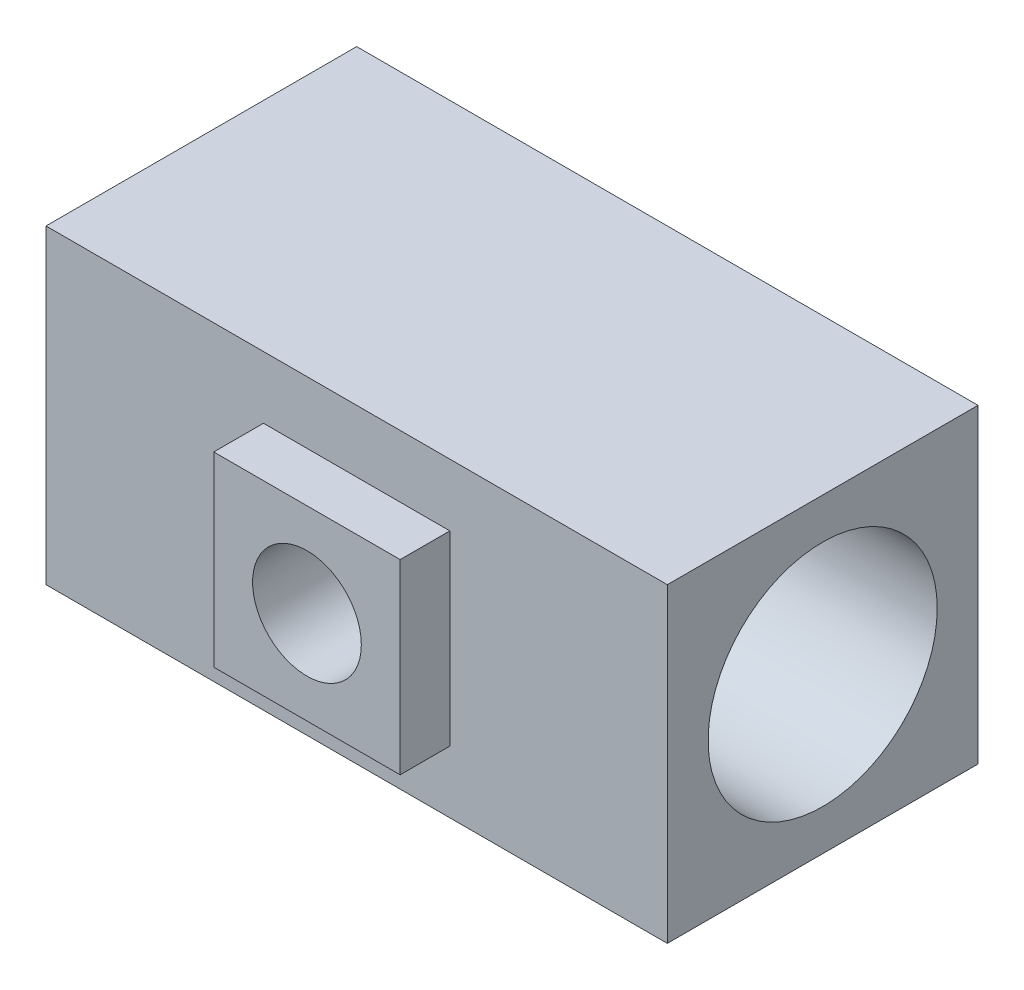
SolidWorks part; units mm, degrees
material "6061 Alloy"
ref_plane "X-Y Datum" through (0, 0, 0) normal (0, 0, 1) x (1, 0, 0)
ref_plane "X-Z Datum" through (0, 0, 0) normal (0, 1, 0) x (1, 0, 0)
ref_plane "Y-Z Datum" through (0, 0, 0) normal (1, 0, 0) x (0, 0, -1)
sketch "Sketch2" plane through (0, 0, 0) normal (0, 1, 0) x (1, 0, 0)
  line L1 (-31.75, -15.875) -> (31.75, -15.875)
  line L2 (-31.75, -15.875) -> (-31.75, 15.875)
  line L3 (-31.75, 15.875) -> (31.75, 15.875)
  line L4 (31.75, -15.875) -> (31.75, 15.875)
  line L5 (-31.75, -15.875) -> (31.75, 15.875) construction
  line L6 (-31.75, 15.875) -> (31.75, -15.875) construction
  point P0 (0, 0)
  dimension "D1" = 31.75
  dimension "D2" = 63.5
extrude "Boss-Extrude1" add sketch "Sketch2" along normal blind 31.75
hole_wizard "59/64 (0.92188) Diameter Hole1" positions "Sketch7" profile "Sketch6" hole size "59/64" standard "ANSI Inch" end condition through all
sketch "Sketch7" plane through (31.75, 0, 0) normal (1, 0, 0) x (0, 0, -1)
  line L0 (-15.875, 31.75) -> (15.875, 0)
  point P0 (0, 15.875)
sketch "Sketch6" plane through (31.75, 15.875, 0) normal (0, 1, 0) x (0, 0, -1)
  line L0 (0, 0) -> (0, 63.5)
  line L1 (0, 63.5) -> (11.7079, 63.5)
  line L2 (11.7079, 63.5) -> (11.7079, 0)
  line L5 (11.7079, 0) -> (0, 0)
  line L11 (0, -6.35) -> (0, 107.95) construction
  dimension "Thru Hole Dia." = 23.4158
  dimension "Thru Hole Depth" = 63.5
sketch "Sketch10" plane through (0, 0, 15.875) normal (0, 0, 1) x (1, 0, 0)
  line L0 (-31.75, 31.75) -> (31.75, 0)
  line L2 (-9.525, 6.35) -> (9.525, 6.35)
  line L3 (-9.525, 6.35) -> (-9.525, 25.4)
  line L4 (-9.525, 25.4) -> (9.525, 25.4)
  line L5 (9.525, 6.35) -> (9.525, 25.4)
  line L6 (-9.525, 6.35) -> (9.525, 25.4) construction
  line L7 (-9.525, 25.4) -> (9.525, 6.35) construction
  point P4 (0, 15.875)
  dimension "D1" = 19.05
  dimension "D2" = 19.05
extrude "Boss-Extrude2" add sketch "Sketch10" along normal blind 5.08 contours L2 L5 L0 L3 | L0 L5 L4 L3
hole_wizard "7/16 (0.4375) Diameter Hole1" positions "Sketch11" profile "Sketch12" hole size "7/16" standard "ANSI Inch"
sketch "Sketch11" plane through (0, 0, 20.955) normal (0, 0, 1) x (1, 0, 0)
  line L0 (-9.525, 25.4) -> (9.525, 6.35)
  point P0 (0, 15.875)
sketch "Sketch12" plane through (0, 15.875, 20.955) normal (1, 0, 0) x (0, -1, 0)
  line L0 (0, 0) -> (0, 28.7385)
  line L1 (0, 28.7385) -> (5.5562, 25.4)
  line L2 (5.5562, 25.4) -> (5.5562, 0)
  line L5 (5.5562, 0) -> (0, 0)
  line L10 (0, 28.7385) -> (-5.5563, 25.4) construction
  line L11 (0, -6.35) -> (0, 107.95) construction
  dimension "Hole Dia." = 11.1125
  dimension "Hole Depth" = 25.4
  dimension "Drill Angle" = 118
thread "Thread1" [suppressed] pitch 1.8143 start angle 0, offset 0, length 15.875, pitch 1.8143, diameter 23.4158
ref_plane "Plane1" through (31.75, 15.875, 11.7079) normal (0, -1, 0) x (0, 0, 1)
sketch "Thread Profile1" plane through (31.75, 15.875, 11.7079) normal (0, -1, 0) x (0, 0, 1)
  line L0 (0, 0) -> (0, 1.8143) construction
  line L1 (0, 0) -> (0.982, 0.567)
  line L2 (0.982, 0.567) -> (0.982, 0.7937)
  line L3 (0.982, 0.7937) -> (0, 1.3607)
  line L4 (0.982, 0.6804) -> (0, 0.6804) construction
  line L11 (0, 0) -> (0, 1.3607)
  point P2 (0, 0)
  dimension "Pitch" = 1.8143
  dimension "Profile_Angle" = 60
  dimension "Profile_Land" = 0.2268
  dimension "Profile_Height" = 0.982
thread "Thread2" [suppressed] pitch 1.8143 start angle 0, offset 0, length 15.875, pitch 1.8143, diameter 23.4158
ref_plane "Plane2" through (-31.75, 15.875, -11.7079) normal (0, -1, 0) x (0, 0, -1)
sketch "Thread Profile2" plane through (-31.75, 15.875, -11.7079) normal (0, -1, 0) x (0, 0, -1)
  line L0 (0, 0) -> (0, 1.8143) construction
  line L1 (0, 0) -> (0.982, 0.567)
  line L2 (0.982, 0.567) -> (0.982, 0.7937)
  line L3 (0.982, 0.7937) -> (0, 1.3607)
  line L4 (0.982, 0.6804) -> (0, 0.6804) construction
  line L11 (0, 0) -> (0, 1.3607)
  point P2 (0, 0)
  dimension "Pitch" = 1.8143
  dimension "Profile_Angle" = 60
  dimension "Profile_Land" = 0.2268
  dimension "Profile_Height" = 0.982
thread "Thread4" [suppressed] pitch 1.8143 start angle 0, offset 0, length 0, pitch 1.8143, diameter 11.1125
ref_plane "Plane4" through (-5.5562, 15.875, 20.955) normal (0, -1, 0) x (-1, 0, 0)
sketch "Thread Profile4" plane through (-5.5562, 15.875, 20.955) normal (0, -1, 0) x (-1, 0, 0)
  line L0 (0, 0) -> (0, 1.8143) construction
  line L1 (0, 0) -> (0.982, 0.567)
  line L2 (0.982, 0.567) -> (0.982, 0.7937)
  line L3 (0.982, 0.7937) -> (0, 1.3607)
  line L4 (0.982, 0.6804) -> (0, 0.6804) construction
  line L11 (0, 0) -> (0, 1.3607)
  point P2 (0, 0)
  dimension "Pitch" = 1.8143
  dimension "Profile_Angle" = 60
  dimension "Profile_Land" = 0.2268
  dimension "Profile_Height" = 0.982
sketch "Sketch13" plane through (-31.75, 0, 0) normal (-1, 0, 0) x (0, 0, 1)
  line L4 (-15.875, 0) -> (15.875, 0)
  line L5 (15.875, 0) -> (15.875, 31.75)
  line L6 (15.875, 31.75) -> (-15.875, 31.75)
  line L7 (-15.875, 31.75) -> (-15.875, 0)
  line L8 (-15.875, 0) -> (15.875, 0)
  line L9 (15.875, 0) -> (15.875, 31.75)
  line L10 (15.875, 31.75) -> (-15.875, 31.75)
  line L11 (-15.875, 31.75) -> (-15.875, 0)
  circle A0 centre (0, 15.875) radius 11.7079 construction
  circle A1 centre (0, 15.875) radius 11.7079 construction
  circle A2 centre (0, 15.875) radius 15.5179
  dimension "D1" = 3.81
  dimension "D2" = 0
extrude "Cut-Extrude1" [suppressed] cut sketch "Sketch13" against normal up to surface (22.225 mm away)
sketch "Sketch14" [suppressed] plane through (31.75, 0, 0) normal (1, 0, 0) x (0, 0, -1)
  line L4 (-15.875, 0) -> (15.875, 0)
  line L5 (15.875, 0) -> (15.875, 31.75)
  line L6 (15.875, 31.75) -> (-15.875, 31.75)
  line L7 (-15.875, 31.75) -> (-15.875, 0)
  line L8 (-15.875, 0) -> (15.875, 0)
  line L9 (15.875, 0) -> (15.875, 31.75)
  line L10 (15.875, 31.75) -> (-15.875, 31.75)
  line L11 (-15.875, 31.75) -> (-15.875, 0)
  circle A2 centre (0, 15.875) radius 15.5179
  circle A3 centre (0, 15.875) radius 15.5179
  dimension "D1" = 0
  dimension "D2" = 3.81
extrude "Cut-Extrude2" [suppressed] cut sketch "Sketch14" against normal up to surface (22.225 mm away)
